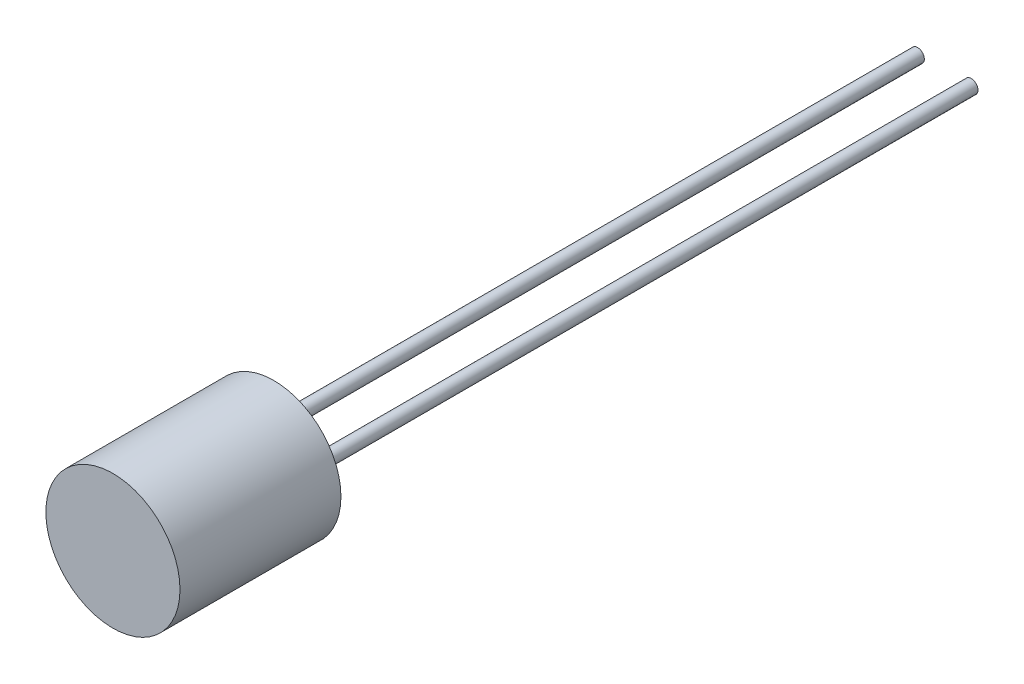
SolidWorks part; units mm, degrees
ref_plane "Front Plane" through (0, 0, 0) normal (0, 0, 1) x (1, 0, 0)
ref_plane "Top Plane" through (0, 0, 0) normal (0, 1, 0) x (1, 0, 0)
ref_plane "Right Plane" through (0, 0, 0) normal (1, 0, 0) x (0, 0, -1)
sketch "Sketch1" plane through (0, 0, 0) normal (0, 0, 1) x (1, 0, 0)
  circle A0 centre (0, 0) radius 2.5
  dimension "D1" = 5
extrude "Boss-Extrude1" add sketch "Sketch1" along normal blind 6
sketch "Sketch2" plane through (0, 0, 0) normal (0, 0, 1) x (1, 0, 0)
  circle A0 centre (-1, 0) radius 0.25
  circle A1 centre (0, 0) radius 2.5 construction
  circle A2 centre (1, 0) radius 0.25
  dimension "D1" = 0.5
  dimension "D2" = 1
  dimension "D3" = 0.5
  dimension "D4" = 1
extrude "Boss-Extrude2" add sketch "Sketch2" against normal blind 25
